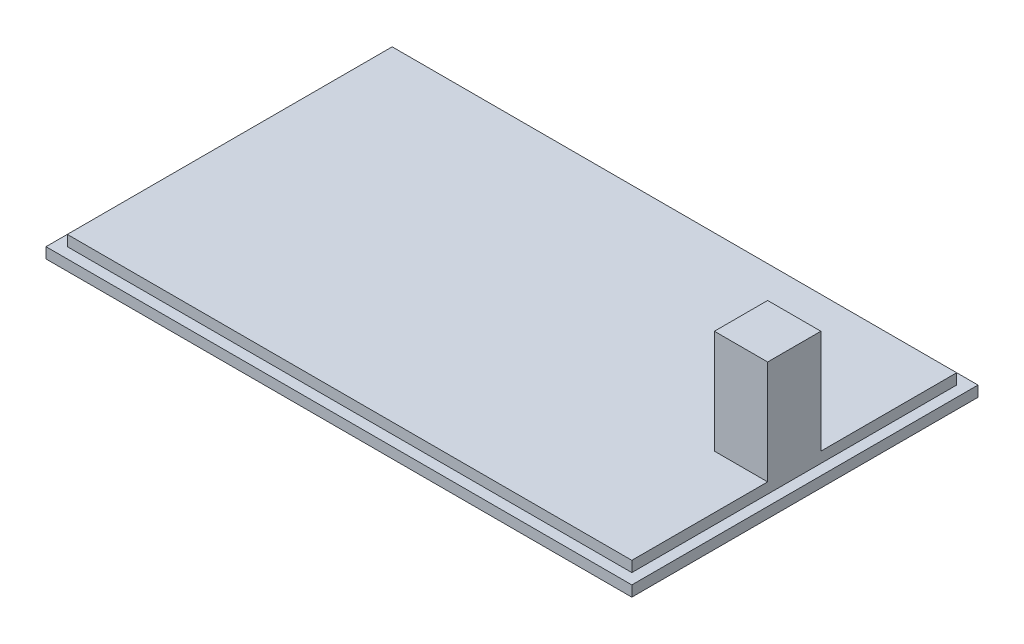
SolidWorks part; units mm, degrees
ref_plane "Front Plane" through (0, 0, 0) normal (0, 0, 1) x (1, 0, 0)
ref_plane "Top Plane" through (0, 0, 0) normal (0, 1, 0) x (1, 0, 0)
ref_plane "Right Plane" through (0, 0, 0) normal (1, 0, 0) x (0, 0, -1)
sketch "Sketch1" plane through (0, 0, 0) normal (0, 1, 0) x (1, 0, 0)
  line L1 (-57.9549, 34.3335) -> (52.0451, 34.3335)
  line L2 (-57.9549, 34.3335) -> (-57.9549, -30.6665)
  line L3 (-57.9549, -30.6665) -> (52.0451, -30.6665)
  line L4 (52.0451, 34.3335) -> (52.0451, -30.6665)
  dimension "D1" = 110
  dimension "D2" = 65
extrude "Boss-Extrude1" add sketch "Sketch1" along normal blind 2
sketch "Sketch2" plane through (0, 2, 0) normal (0, 1, 0) x (1, 0, 0)
  line L0 (-57.9549, 34.3335) -> (-57.9549, -30.6665) construction
  line L1 (-55.9549, 32.3335) -> (50.0451, 32.3335)
  line L2 (-55.9549, 32.3335) -> (-55.9549, -28.6665)
  line L3 (-55.9549, -28.6665) -> (50.0451, -28.6665)
  line L4 (50.0451, 32.3335) -> (50.0451, -28.6665)
  line L5 (-57.9549, -30.6665) -> (52.0451, -30.6665) construction
  line L6 (52.0451, -30.6665) -> (52.0451, 34.3335) construction
  line L7 (52.0451, 34.3335) -> (-57.9549, 34.3335) construction
  dimension "D1" = 2
  dimension "D2" = 2
  dimension "D3" = 2
  dimension "D4" = 2
extrude "Boss-Extrude3" add sketch "Sketch2" along normal blind 2 contours L2 L3 L4 L1
sketch "Sketch6" plane through (0, 4, 0) normal (0, 1, 0) x (1, 0, 0)
  line L0 (50.0451, 32.3335) -> (50.0451, -28.6665) construction
  line L1 (50.0451, 6.8335) -> (40.0451, 6.8335)
  line L2 (50.0451, 6.8335) -> (50.0451, -3.1665)
  line L3 (50.0451, -3.1665) -> (40.0451, -3.1665)
  line L4 (40.0451, 6.8335) -> (40.0451, -3.1665)
  line L8 (-55.9549, -28.6665) -> (50.0451, -28.6665) construction
  dimension "D1" = 10
  dimension "D2" = 10
  dimension "D3" = 25.5
extrude "Boss-Extrude4" add sketch "Sketch6" along normal blind 19.5 contours L3 L4 L1 L2
equation "\"boxlengthout\"=180"
equation "\"boxwidthout\"= 120"
equation "\"board_arduinoheight\"= 24"
equation "\"boardwidth\"= 60"
equation "\"boardlength\"= 77"
equation "\"batterylength\"= 48"
equation "\"batterywidth\"= 25"
equation "\"batteryheight\"= 15"
equation "\"boxthickenss\"= 2"
equation "\"dividerheight\"=5"
equation "\"D1@Sketch1\"=\"boardlength\"+\"batterywidth\"+3*\"boxthickenss\"+2"
equation "\"D2@Sketch1\"=\"boardwidth\"+\"boxthickenss\"*2+1"
equation "\"D1@Boss-Extrude1\"=\"boxthickenss\""
equation "\"D1@Sketch2\"=\"lid_separation\""
equation "\"lid_separation\" = 2"
equation "\"D2@Sketch2\"=\"lid_separation\""
equation "\"D3@Sketch2\"=\"lid_separation\""
equation "\"lid_depth\"= 2"
equation "\"D1@Boss-Extrude3\"=\"lid_depth\""
equation "\"battery_to_top\"= 19.5"
equation "\"spacer_dim\"= 10"
equation "\"D1@Sketch6\"=\"spacer_dim\""
equation "\"D2@Sketch6\"=\"spacer_dim\""
equation "\"D3@Sketch6\"=(\"RD1@Annotations\"-\"D2@Sketch6\")/2"
equation "\"D1@Boss-Extrude4\"=\"battery_to_top\""
